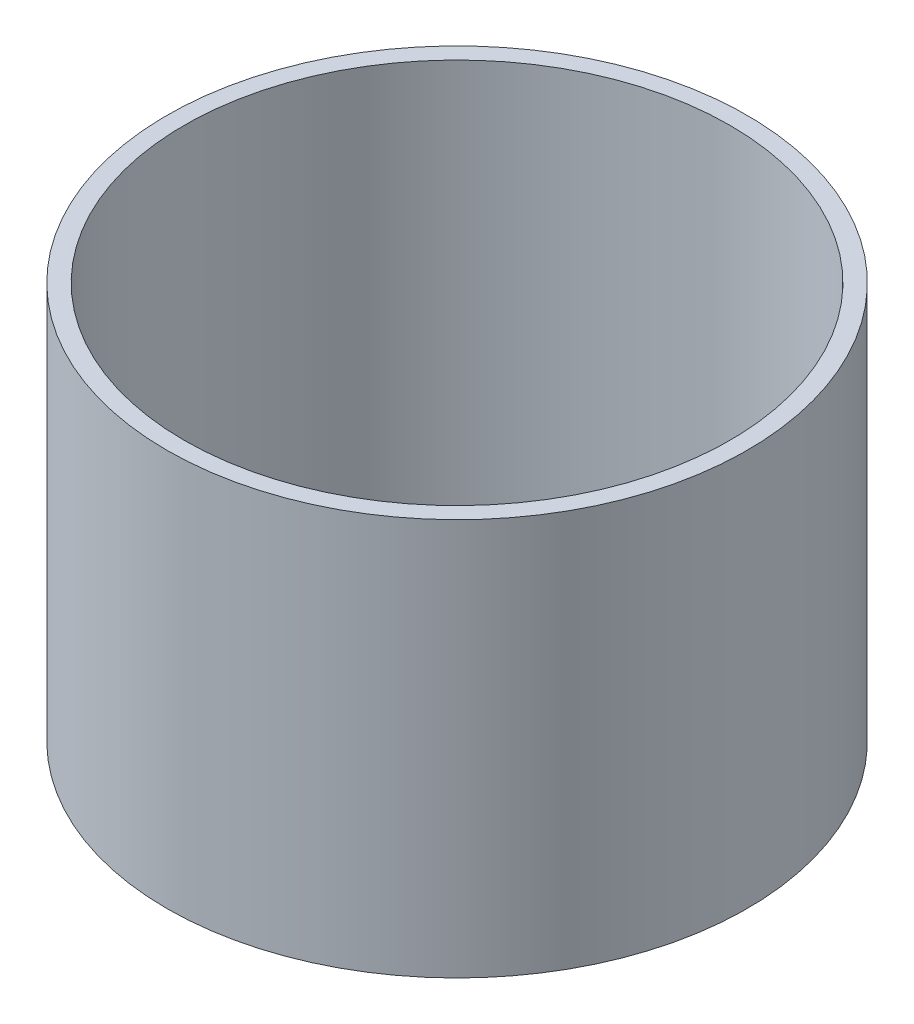
SolidWorks part; units mm, degrees
ref_plane "Front" through (0, 0, 0) normal (0, 0, 1) x (1, 0, 0)
ref_plane "Top" through (0, 0, 0) normal (0, 1, 0) x (1, 0, 0)
ref_plane "Right" through (0, 0, 0) normal (1, 0, 0) x (0, 0, -1)
sketch "Sketch7" plane through (0, 0, 0) normal (0, 1, 0) x (1, 0, 0)
  circle A0 centre (0, 0) radius 27.5
  circle A1 centre (0, 0) radius 29.2395
  dimension "D1" = 55
extrude "Boss-Extrude1" add sketch "Sketch7" against normal blind 40 contours A1 A0
